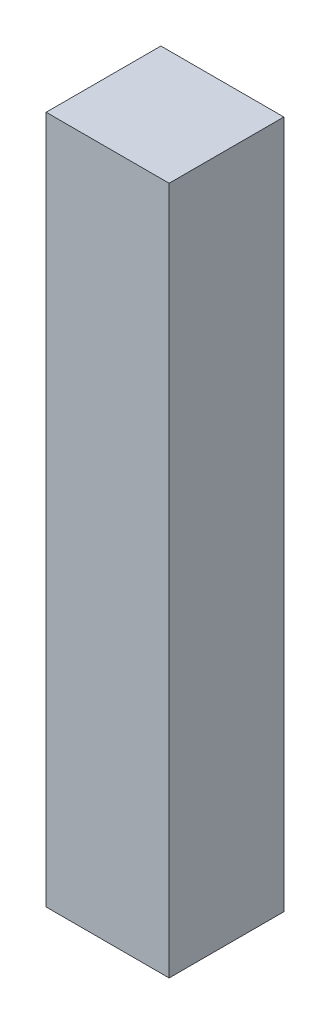
SolidWorks part; units mm, degrees
ref_plane "Front Plane" through (0, 0, 0) normal (0, 0, 1) x (1, 0, 0)
ref_plane "Top Plane" through (0, 0, 0) normal (0, 1, 0) x (1, 0, 0)
ref_plane "Right Plane" through (0, 0, 0) normal (1, 0, 0) x (0, 0, -1)
sketch "Sketch1" plane through (0, 0, 0) normal (0, 0, 1) x (1, 0, 0)
  line L1 (0, 0) -> (3.4036, 0)
  line L2 (0, 0) -> (0, -19.05)
  line L3 (0, -19.05) -> (3.4036, -19.05)
  line L4 (3.4036, 0) -> (3.4036, -19.05)
  dimension "D1" = 19.05
  dimension "D2" = 3.4036
extrude "Boss-Extrude1" add sketch "Sketch1" along normal blind 3.175
